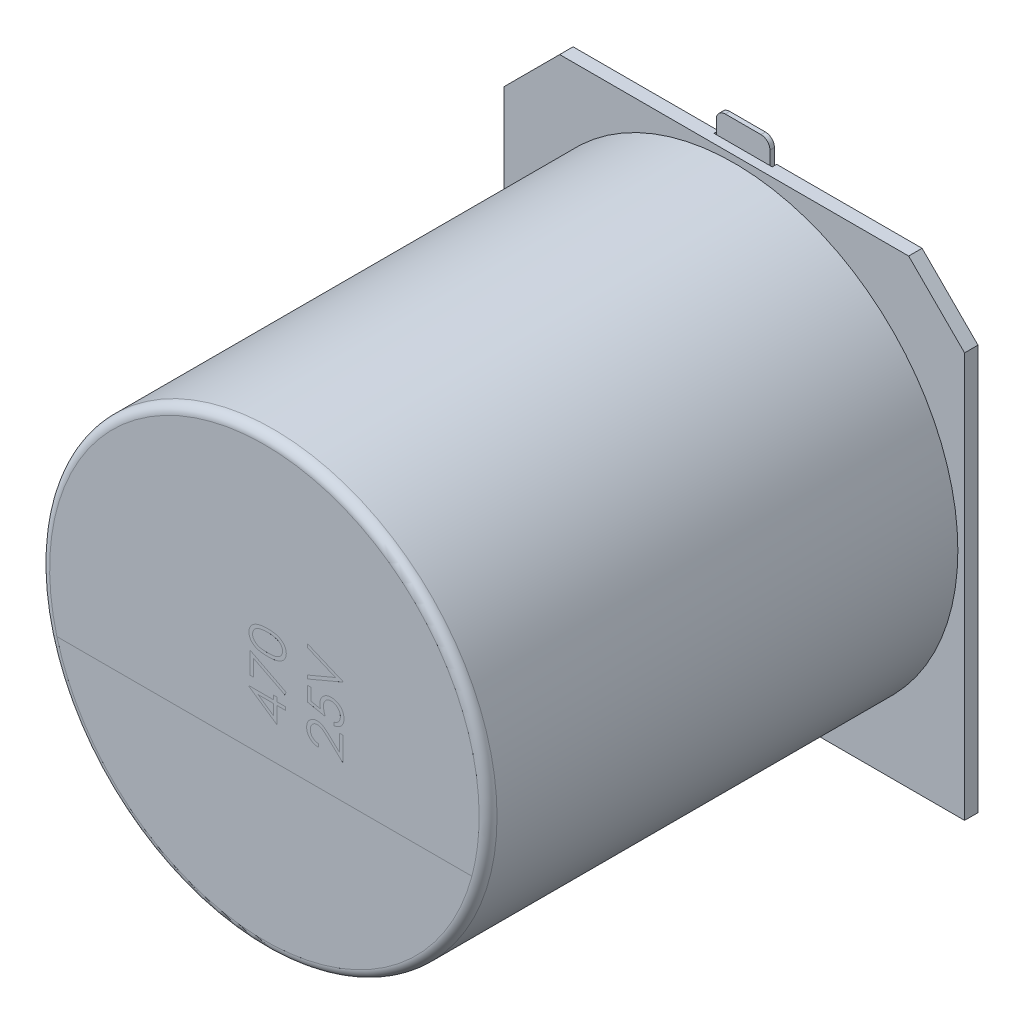
SolidWorks part; units mm, degrees
ref_plane "Frontal" through (0, 0, 0) normal (0, 0, 1) x (1, 0, 0)
ref_plane "Superior" through (0, 0, 0) normal (0, 1, 0) x (1, 0, 0)
ref_plane "Direito" through (0, 0, 0) normal (1, 0, 0) x (0, 0, -1)
sketch "Esboço1" plane through (0, 0, 0) normal (0, 0, 1) x (1, 0, 0)
  line L0 (-5.15, 3.9) -> (-3.9, 5.15)
  line L1 (-3.9, 5.15) -> (3.9, 5.15)
  line L2 (-5.15, 3.9) -> (-5.15, -5.15)
  line L3 (-5.15, -5.15) -> (5.15, -5.15)
  line L4 (5.15, 3.9) -> (5.15, -5.15)
  line L5 (-5.15, 5.15) -> (5.15, -5.15) construction
  line L6 (-5.15, -5.15) -> (5.15, 5.15) construction
  line L7 (3.9, 5.15) -> (5.15, 3.9)
  point P0 (0, 0)
  dimension "D1" = 10.3
  dimension "D2" = 10.3
extrude "Ressalto-extrusão1" add sketch "Esboço1" along normal blind 0.3
sketch "Esboço2" plane through (0, 0, 0.3) normal (0, 0, 1) x (1, 0, 0)
  circle A0 centre (0, 0) radius 5
  dimension "D1" = 10
extrude "Ressalto-extrusão2" add sketch "Esboço2" along normal blind 10.5 separate body
fillet "Filete1" radius 0.2 1 edges at (5, 0, 10.8)
sketch "Esboço3" plane through (0, 0, 10.8) normal (0, 0, 1) x (1, 0, 0)
  line L0 (-4.6382, -1.2358) -> (4.6382, -1.2358)
  circle A0 centre (0, 0) radius 4.8 construction
  arc A1 (-4.6382, -1.2358) -> (4.6382, -1.2358) centre (0, 0) ccw
extrude "Corte-extrusão1" cut sketch "Esboço3" against normal blind 0.0001
sketch "Esboço4" plane through (0, 0, 10.8) normal (0, 0, 1) x (1, 0, 0)
  line L0 (0.4685, -0.5169) -> (0.4685, 1.9526) construction
  line L1 (1.7582, -0.5169) -> (1.7582, 1.8446) construction
  text T0 "470" font "Century Gothic" height in points 3
  text T1 "25V" font "Century Gothic" height in points 3
extrude "Corte-extrusão2" cut sketch "Esboço4" against normal blind 0.0001
sketch "Esboço5" plane through (0, 0, 0) normal (0, 0, -1) x (-1, 0, 0)
  line L0 (0, 4.05) -> (0, 0) construction
  line L1 (-0.65, 5.65) -> (0.65, 5.65)
  line L2 (-0.65, 5.65) -> (-0.65, 2.45)
  line L3 (-0.65, 2.45) -> (0.65, 2.45)
  line L4 (0.65, 5.65) -> (0.65, 2.45)
  line L5 (-0.65, 5.65) -> (0.65, 2.45) construction
  line L6 (-0.65, 2.45) -> (0.65, 5.65) construction
  line L7 (-3.9, 5.15) -> (3.9, 5.15) construction
  line L8 (0, 0) -> (5.286, 0) construction
  line L9 (-0.65, -2.45) -> (0.65, -2.45)
  line L10 (0.65, -5.65) -> (0.65, -2.45)
  line L11 (-0.65, -5.65) -> (-0.65, -2.45)
  line L12 (-0.65, -5.65) -> (0.65, -5.65)
  point P0 (0, 4.05)
  dimension "D1" = 0.5
  dimension "D2" = 3.2
  dimension "D3" = 1.3
extrude "Corte-extrusão3" cut sketch "Esboço5" against normal blind 0.1
sketch "Esboço6" plane through (0, 0, 0.1) normal (0, 0, -1) x (-1, 0, 0)
  line L0 (-0.65, 2.45) -> (0.65, 2.45) construction
  line L1 (-0.4, 5.65) -> (0.4, 5.65)
  line L2 (-0.6, 5.45) -> (-0.6, 2.45)
  line L3 (-0.6, 2.45) -> (0.6, 2.45)
  line L4 (0.6, 5.45) -> (0.6, 2.45)
  line L5 (-0.6, 5.65) -> (0.6, 2.45) construction
  line L6 (-0.6, 2.45) -> (0.6, 5.65) construction
  line L7 (0, 4.05) -> (0, 0) construction
  line L8 (0.65, 5.15) -> (-0.65, 5.15) construction
  line L9 (0, 0) -> (6.6324, 0) construction
  line L10 (-0.6, -2.45) -> (0.6, -2.45)
  line L11 (-0.6, -5.45) -> (-0.6, -2.45)
  line L12 (0.6, -5.45) -> (0.6, -2.45)
  line L13 (-0.4, -5.65) -> (0.4, -5.65)
  arc A0 (0.4, 5.65) -> (0.6, 5.45) centre (0.4, 5.45) cw
  arc A1 (-0.4, 5.65) -> (-0.6, 5.45) centre (-0.4, 5.45) ccw
  arc A2 (0.4, -5.65) -> (0.6, -5.45) centre (0.4, -5.45) ccw
  arc A3 (-0.4, -5.65) -> (-0.6, -5.45) centre (-0.4, -5.45) cw
  point P0 (0, 4.05)
  dimension "D3" = 0.2
  dimension "D1" = 1.2
  dimension "D2" = 0.5
extrude "Ressalto-extrusão3" add sketch "Esboço6" along normal up to surface (0.1 mm away) separate body up to face at (0, 0.5571, 0)
